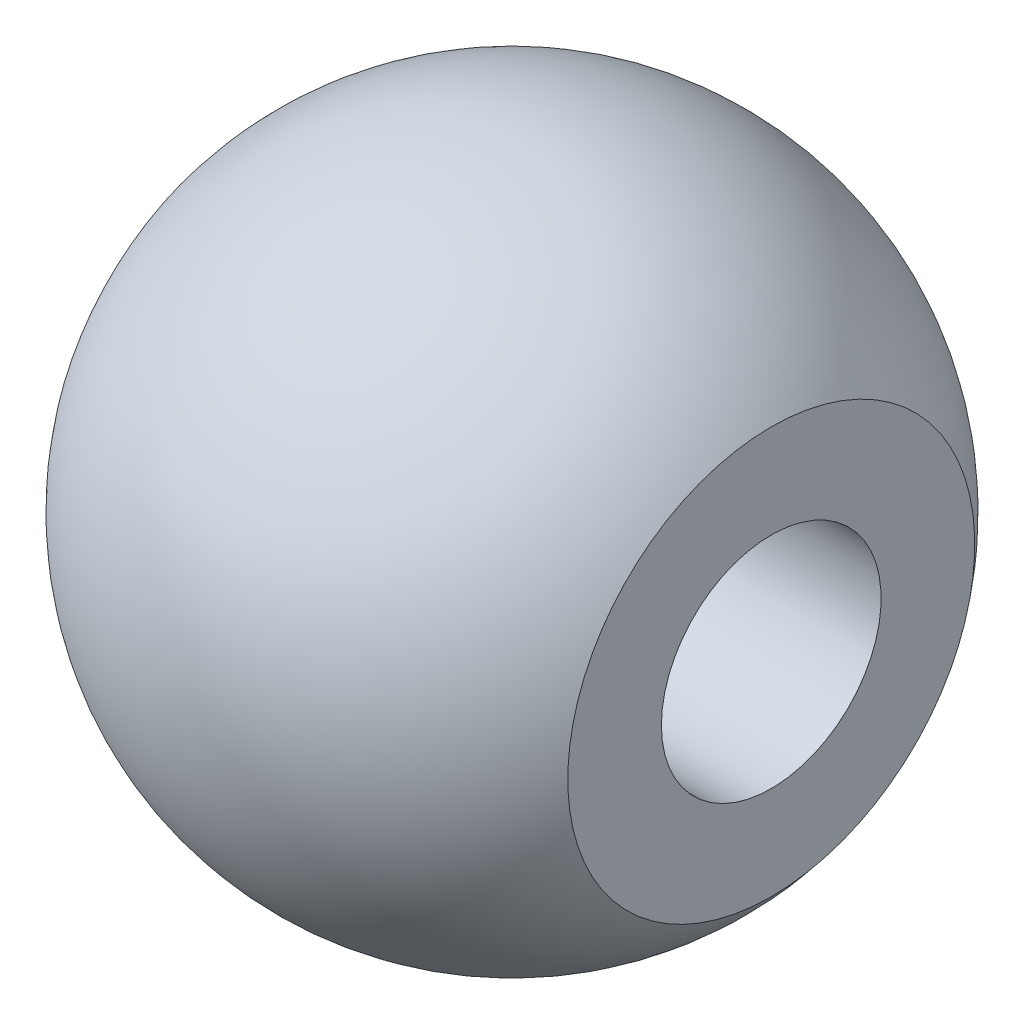
SolidWorks part; units mm, degrees
ref_plane "Front" through (0, 0, 0) normal (0, 0, 1) x (1, 0, 0)
ref_plane "Top" through (0, 0, 0) normal (0, 1, 0) x (1, 0, 0)
ref_plane "Right" through (0, 0, 0) normal (1, 0, 0) x (0, 0, -1)
sketch "Sketch1" plane through (0, 0, 0) normal (0, 0, 1) x (1, 0, 0)
  line L0 (-6, 0) -> (6, 0)
  line L1 (-13.6012, 0) -> (14.8716, 0) construction
  arc A0 (6, 0) -> (-6, 0) centre (0, 0) ccw
  dimension "D1" = 6
revolve "Revolve1" add sketch "Sketch1" angle 360 about L1
sketch "Sketch2" plane through (0, 0, 0) normal (0, 0, 1) x (1, 0, 0)
  line L0 (0, 13.8825) -> (0, -14.5754) construction
  line L1 (-4.72, 3.7043) -> (-4.72, -3.7043)
  line L2 (4.72, 3.7043) -> (4.72, -3.7043)
  circle A0 centre (0, 0) radius 6 construction
  arc A1 (-4.72, 3.7043) -> (-4.72, -3.7043) centre (0, 0) ccw
  arc A2 (4.72, -3.7043) -> (4.72, 3.7043) centre (0, 0) ccw
  dimension "D1" = 9.44
extrude "Cut-Extrude2" cut sketch "Sketch2" against normal through all and the other way through all
sketch "Sketch3" plane through (0, 0, 0) normal (0, 0, 1) x (1, 0, 0)
  line L0 (-7.0105, 0) -> (8.1424, 0) construction
  line L1 (-4.72, 3.44) -> (-3.28, 2)
  line L2 (-4.72, 3.7043) -> (-4.72, -3.7043) construction
  line L3 (-3.28, 2) -> (4.72, 2)
  line L4 (4.72, -3.7043) -> (4.72, 3.7043) construction
  line L5 (4.72, 2) -> (4.72, 0)
  line L6 (4.72, 0) -> (-4.72, 0)
  line L7 (-4.72, 0) -> (-4.72, 3.44)
  dimension "D1" = 4
  dimension "D2" = 45
  dimension "D3" = 1.44
revolve "Cut-Revolve1" cut sketch "Sketch3" angle 360 about L0
